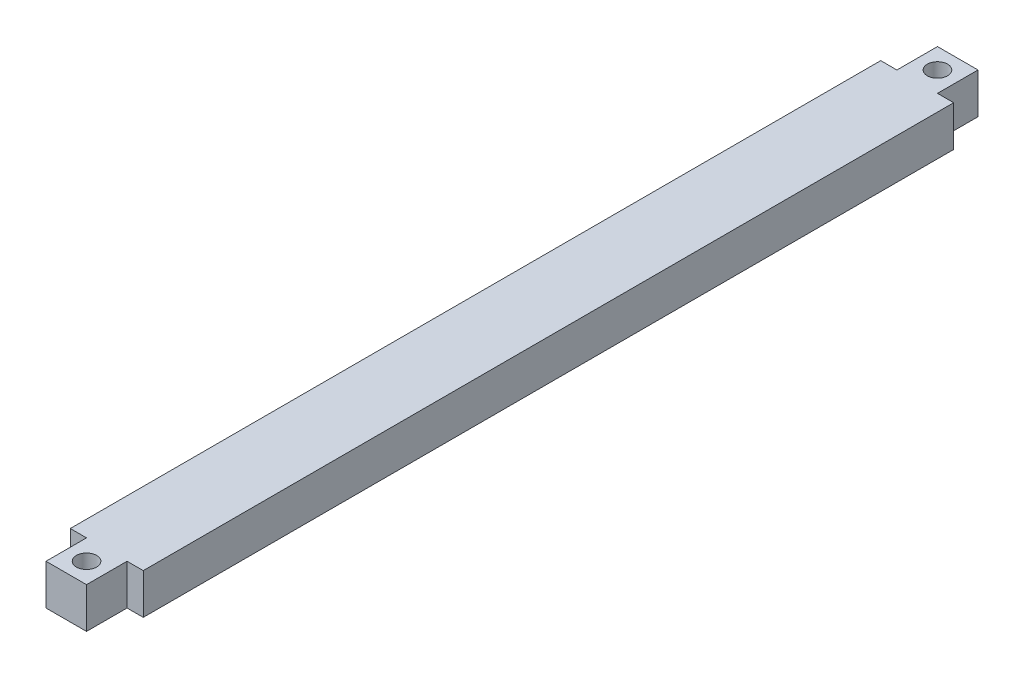
SolidWorks part; units mm, degrees
ref_plane "Front Plane" through (0, 0, 0) normal (0, 0, 1) x (1, 0, 0)
ref_plane "Top Plane" through (0, 0, 0) normal (0, 1, 0) x (1, 0, 0)
ref_plane "Right Plane" through (0, 0, 0) normal (1, 0, 0) x (0, 0, -1)
sketch "Sketch1" plane through (0, 0, 0) normal (0, 0, 1) x (1, 0, 0)
  line L1 (0.4385, 1.0129) -> (5.4385, 1.0129)
  line L2 (0.4385, 1.0129) -> (0.4385, -3.9871)
  line L3 (0.4385, -3.9871) -> (5.4385, -3.9871)
  line L4 (5.4385, 1.0129) -> (5.4385, -3.9871)
  dimension "D1" = 5
  dimension "D2" = 5
extrude "Boss-Extrude1" add sketch "Sketch1" along normal blind 110
sketch "Sketch2" plane through (0, 1.0129, 0) normal (0, 1, 0) x (1, 0, 0)
  line L0 (5.4385, -5) -> (7.4385, -5)
  line L1 (5.4385, -110) -> (5.4385, 0) construction
  line L2 (18.8139, -5) -> (5.4385, -5) construction
  line L3 (7.4385, -5) -> (7.4385, -105)
  line L4 (18.8139, -105) -> (5.4385, -105) construction
  line L5 (7.4385, -105) -> (5.4385, -105)
  line L6 (5.4385, -105) -> (5.4385, -5)
  dimension "D1" = 2
extrude "Boss-Extrude2" add sketch "Sketch2" against normal blind 5
sketch "Sketch3" plane through (0, 1.0129, 0) normal (0, 1, 0) x (1, 0, 0)
  line L0 (0.4385, -5.0091) -> (-1.5615, -5)
  line L1 (0.4385, -110) -> (0.4385, 0) construction
  line L2 (0.4385, -5) -> (-12.1137, -5) construction
  line L3 (-1.5615, -5) -> (-1.5615, -105)
  line L4 (0.4385, -105) -> (-12.1137, -105) construction
  line L5 (-1.5615, -105) -> (0.4385, -105)
  line L6 (0.4385, -105) -> (0.4385, -5.0091)
  dimension "D1" = 2
extrude "Boss-Extrude3" add sketch "Sketch3" against normal blind 5 contours L3 L5 L6 L0
sketch "Sketch4" plane through (0, 1.0129, 0) normal (0, 1, 0) x (1, 0, 0)
  line L0 (5.4385, -2.5) -> (0.4385, -2.5045) construction
  line L1 (5.4385, -5) -> (5.4385, 0) construction
  line L2 (0.4385, -5.0091) -> (0.4385, 0) construction
  line L3 (2.9385, 0) -> (2.9385, -2.5023) construction
  line L4 (5.4385, 0) -> (0.4385, 0) construction
  line L5 (-1.5615, -55) -> (7.4385, -55) construction
  line L6 (-1.5615, -5) -> (-1.5615, -105) construction
  line L7 (7.4385, -105) -> (7.4385, -5) construction
sketch "Sketch5" plane through (7.4385, 0, 0) normal (1, 0, 0) x (0, 0, -1)
  line L0 (-55, 1.0129) -> (-55, -3.9871) construction
  line L1 (-105, -3.9871) -> (-5, -3.9871) construction
ref_plane "Plane1" through (0, 0, 55) normal (0, 0, -1) x (-1, 0, 0)
hole_wizard "M3 Tapped Hole1" positions "Sketch7" profile "Sketch6" tap size "M3" standard "ISO"
sketch "Sketch7" plane through (0, 1.0129, 0) normal (0, 1, 0) x (1, 0, 0)
  point P0 (2.9385, -2.5023)
sketch "Sketch6" plane through (2.9385, 1.0129, 2.5023) normal (1, 0, 0) x (0, 0, 1)
  line L0 (0, 0) -> (0, 8.7511)
  line L1 (0, 8.7511) -> (1.25, 8)
  line L2 (1.25, 8) -> (1.25, 0)
  line L5 (1.25, 0) -> (0, 0)
  line L10 (0, 8.7511) -> (-1.25, 8) construction
  line L11 (0, -6.35) -> (0, 107.95) construction
  dimension "Tap Drill Dia." = 2.5
  dimension "Tap Drill Depth" = 8
  dimension "Drill Angle" = 118
mirror "Mirror1" about plane through (0, 0, 55) normal (0, 0, -1) of "M3 Tapped Hole1"
